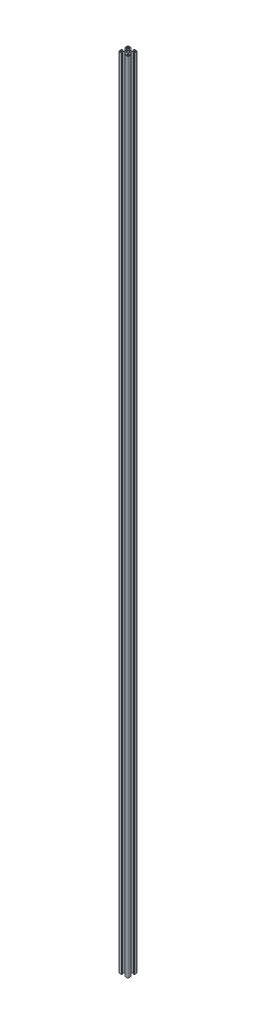
SolidWorks part; units mm, degrees
material "6063-T5"
ref_plane "前视基准面" through (0, 0, 0) normal (0, 0, 1) x (1, 0, 0)
ref_plane "上视基准面" through (0, 0, 0) normal (0, 1, 0) x (1, 0, 0)
ref_plane "右视基准面" through (0, 0, 0) normal (1, 0, 0) x (0, 0, -1)
sketch "草图3" plane through (0, 0, 0) normal (0, 1, 0) x (1, 0, 0)
  line L0 (0, 0) -> (-15, -15) construction
  line L1 (-15, -15) -> (-15, 0) construction
  line L2 (-15, 0) -> (0, 0) construction
  line L3 (-15, -12.5) -> (-15, -5.4)
  line L4 (-14.8, -5.2) -> (-14.4, -5.2)
  line L5 (-14.2, -5) -> (-14.2, -4.3)
  line L6 (-14, -4.1) -> (-13.2, -4.1)
  line L7 (-13.2, -4.1) -> (-13.2, -8.25)
  line L8 (-13.2, -8.25) -> (-9.5228, -8.25)
  line L9 (-9.5228, -8.25) -> (-5.8, -4.5272)
  line L10 (-5.8, -4.5272) -> (-5.8, 4.5272)
  line L11 (-13.2, -12.2) -> (-13.2, -11.05)
  line L12 (-12.2, -10.05) -> (-11.05, -10.05)
  line L13 (-4.5272, -5.8) -> (4.5272, -5.8)
  line L14 (-8.25, -9.5228) -> (-4.5272, -5.8)
  line L15 (-12.2, -13.2) -> (-11.05, -13.2)
  line L16 (-10.05, -12.2) -> (-10.05, -11.05)
  line L17 (-5.2, -14.8) -> (-5.2, -14.4)
  line L18 (-5, -14.2) -> (-4.3, -14.2)
  line L19 (-4.1, -14) -> (-4.1, -13.2)
  line L20 (-4.1, -13.2) -> (-8.25, -13.2)
  line L21 (-8.25, -13.2) -> (-8.25, -9.5228)
  line L22 (-12.5, -15) -> (-5.4, -15)
  line L23 (-12.5, 15) -> (-5.4, 15)
  line L24 (-8.25, 13.2) -> (-8.25, 9.5228)
  line L25 (-4.1, 13.2) -> (-8.25, 13.2)
  line L26 (-4.1, 14) -> (-4.1, 13.2)
  line L27 (-5, 14.2) -> (-4.3, 14.2)
  line L28 (-5.2, 14.8) -> (-5.2, 14.4)
  line L29 (-10.05, 12.2) -> (-10.05, 11.05)
  line L30 (-12.2, 13.2) -> (-11.05, 13.2)
  line L31 (-8.25, 9.5228) -> (-4.5272, 5.8)
  line L32 (-4.5272, 5.8) -> (4.5272, 5.8)
  line L33 (-12.2, 10.05) -> (-11.05, 10.05)
  line L34 (-13.2, 12.2) -> (-13.2, 11.05)
  line L35 (-9.5228, 8.25) -> (-5.8, 4.5272)
  line L36 (-13.2, 8.25) -> (-9.5228, 8.25)
  line L37 (-13.2, 4.1) -> (-13.2, 8.25)
  line L38 (-14, 4.1) -> (-13.2, 4.1)
  line L39 (-14.2, 5) -> (-14.2, 4.3)
  line L40 (-14.8, 5.2) -> (-14.4, 5.2)
  line L41 (-15, 12.5) -> (-15, 5.4)
  line L42 (0, 0) -> (0, -12.3268) construction
  line L43 (15, 12.5) -> (15, 5.4)
  line L44 (14.8, 5.2) -> (14.4, 5.2)
  line L45 (14.2, 5) -> (14.2, 4.3)
  line L46 (14, 4.1) -> (13.2, 4.1)
  line L47 (13.2, 4.1) -> (13.2, 8.25)
  line L48 (13.2, 8.25) -> (9.5228, 8.25)
  line L49 (9.5228, 8.25) -> (5.8, 4.5272)
  line L50 (13.2, 12.2) -> (13.2, 11.05)
  line L51 (12.2, 10.05) -> (11.05, 10.05)
  line L52 (8.25, 9.5228) -> (4.5272, 5.8)
  line L53 (12.2, 13.2) -> (11.05, 13.2)
  line L54 (10.05, 12.2) -> (10.05, 11.05)
  line L55 (5.2, 14.8) -> (5.2, 14.4)
  line L56 (5, 14.2) -> (4.3, 14.2)
  line L57 (4.1, 14) -> (4.1, 13.2)
  line L58 (4.1, 13.2) -> (8.25, 13.2)
  line L59 (8.25, 13.2) -> (8.25, 9.5228)
  line L60 (12.5, 15) -> (5.4, 15)
  line L61 (12.5, -15) -> (5.4, -15)
  line L62 (8.25, -13.2) -> (8.25, -9.5228)
  line L63 (4.1, -13.2) -> (8.25, -13.2)
  line L64 (4.1, -14) -> (4.1, -13.2)
  line L65 (5, -14.2) -> (4.3, -14.2)
  line L66 (5.2, -14.8) -> (5.2, -14.4)
  line L67 (10.05, -12.2) -> (10.05, -11.05)
  line L68 (12.2, -13.2) -> (11.05, -13.2)
  line L69 (8.25, -9.5228) -> (4.5272, -5.8)
  line L70 (12.2, -10.05) -> (11.05, -10.05)
  line L71 (13.2, -12.2) -> (13.2, -11.05)
  line L72 (5.8, -4.5272) -> (5.8, 4.5272)
  line L73 (9.5228, -8.25) -> (5.8, -4.5272)
  line L74 (13.2, -8.25) -> (9.5228, -8.25)
  line L75 (13.2, -4.1) -> (13.2, -8.25)
  line L76 (14, -4.1) -> (13.2, -4.1)
  line L77 (14.2, -5) -> (14.2, -4.3)
  line L78 (14.8, -5.2) -> (14.4, -5.2)
  line L79 (15, -12.5) -> (15, -5.4)
  circle A0 centre (0, 0) radius 3.4
  arc A1 (-12.5, 15) -> (-15, 12.5) centre (-12.5, 12.5) ccw
  arc A2 (15, 12.5) -> (12.5, 15) centre (12.5, 12.5) ccw
  arc A3 (12.5, -15) -> (15, -12.5) centre (12.5, -12.5) ccw
  arc A4 (-15, -12.5) -> (-12.5, -15) centre (-12.5, -12.5) ccw
  arc A5 (-12.2, 13.2) -> (-13.2, 12.2) centre (-12.2, 12.2) ccw
  arc A6 (-12.2, 10.05) -> (-13.2, 11.05) centre (-12.2, 11.05) cw
  arc A7 (-10.05, 11.05) -> (-11.05, 10.05) centre (-11.05, 11.05) cw
  arc A8 (-10.05, 12.2) -> (-11.05, 13.2) centre (-11.05, 12.2) ccw
  arc A9 (11.05, 10.05) -> (10.05, 11.05) centre (11.05, 11.05) cw
  arc A10 (11.05, 13.2) -> (10.05, 12.2) centre (11.05, 12.2) ccw
  arc A11 (13.2, 12.2) -> (12.2, 13.2) centre (12.2, 12.2) ccw
  arc A12 (13.2, 11.05) -> (12.2, 10.05) centre (12.2, 11.05) cw
  arc A13 (12.2, -10.05) -> (13.2, -11.05) centre (12.2, -11.05) cw
  arc A14 (10.05, -11.05) -> (11.05, -10.05) centre (11.05, -11.05) cw
  arc A15 (10.05, -12.2) -> (11.05, -13.2) centre (11.05, -12.2) ccw
  arc A16 (12.2, -13.2) -> (13.2, -12.2) centre (12.2, -12.2) ccw
  arc A17 (-13.2, -11.05) -> (-12.2, -10.05) centre (-12.2, -11.05) cw
  arc A18 (-11.05, -10.05) -> (-10.05, -11.05) centre (-11.05, -11.05) cw
  arc A19 (-11.05, -13.2) -> (-10.05, -12.2) centre (-11.05, -12.2) ccw
  arc A20 (-13.2, -12.2) -> (-12.2, -13.2) centre (-12.2, -12.2) ccw
  arc A21 (-15, -5.4) -> (-14.8, -5.2) centre (-14.8, -5.4) cw
  arc A22 (-14.4, -5.2) -> (-14.2, -5) centre (-14.4, -5) ccw
  arc A23 (-14.2, -4.3) -> (-14, -4.1) centre (-14, -4.3) cw
  arc A24 (-14, 4.1) -> (-14.2, 4.3) centre (-14, 4.3) cw
  arc A25 (-14.2, 5) -> (-14.4, 5.2) centre (-14.4, 5) ccw
  arc A26 (-14.8, 5.2) -> (-15, 5.4) centre (-14.8, 5.4) cw
  arc A27 (-5.4, 15) -> (-5.2, 14.8) centre (-5.4, 14.8) cw
  arc A28 (-5, 14.2) -> (-5.2, 14.4) centre (-5, 14.4) cw
  arc A29 (-4.1, 14) -> (-4.3, 14.2) centre (-4.3, 14) ccw
  arc A30 (5.2, 14.8) -> (5.4, 15) centre (5.4, 14.8) cw
  arc A31 (5.2, 14.4) -> (5, 14.2) centre (5, 14.4) cw
  arc A32 (4.3, 14.2) -> (4.1, 14) centre (4.3, 14) ccw
  arc A33 (15, 5.4) -> (14.8, 5.2) centre (14.8, 5.4) cw
  arc A34 (14.4, 5.2) -> (14.2, 5) centre (14.4, 5) ccw
  arc A35 (14.2, 4.3) -> (14, 4.1) centre (14, 4.3) cw
  arc A36 (14, -4.1) -> (14.2, -4.3) centre (14, -4.3) cw
  arc A37 (14.2, -5) -> (14.4, -5.2) centre (14.4, -5) ccw
  arc A38 (14.8, -5.2) -> (15, -5.4) centre (14.8, -5.4) cw
  arc A39 (5.4, -15) -> (5.2, -14.8) centre (5.4, -14.8) cw
  arc A40 (5, -14.2) -> (5.2, -14.4) centre (5, -14.4) cw
  arc A41 (4.1, -14) -> (4.3, -14.2) centre (4.3, -14) ccw
  arc A42 (-5.2, -14.4) -> (-5, -14.2) centre (-5, -14.4) cw
  arc A43 (-4.3, -14.2) -> (-4.1, -14) centre (-4.3, -14) ccw
  arc A44 (-5.2, -14.8) -> (-5.4, -15) centre (-5.4, -14.8) cw
  point P38 (-5.8, 0)
  point P46 (0, 5.8)
  point P47 (0, -5.8)
  point P83 (5.8, 0)
  point P87 (-15, 15)
  point P90 (15, 15)
  point P93 (15, -15)
  point P99 (-13.2, 13.2)
  point P102 (-13.2, 10.05)
  point P105 (-10.05, 10.05)
  point P108 (-10.05, 13.2)
  point P111 (10.05, 10.05)
  point P114 (10.05, 13.2)
  point P117 (13.2, 13.2)
  point P120 (13.2, 10.05)
  point P123 (13.2, -10.05)
  point P126 (10.05, -10.05)
  point P129 (10.05, -13.2)
  point P132 (13.2, -13.2)
  point P135 (-13.2, -10.05)
  point P138 (-10.05, -10.05)
  point P141 (-10.05, -13.2)
  point P144 (-13.2, -13.2)
  point P147 (-15, -5.2)
  point P150 (-14.2, -5.2)
  point P153 (-14.2, -4.1)
  point P156 (-14.2, 4.1)
  point P159 (-14.2, 5.2)
  point P162 (-15, 5.2)
  point P165 (-5.2, 15)
  point P168 (-5.2, 14.2)
  point P171 (-4.1, 14.2)
  point P174 (5.2, 15)
  point P177 (5.2, 14.2)
  point P180 (4.1, 14.2)
  point P183 (15, 5.2)
  point P186 (14.2, 5.2)
  point P189 (14.2, 4.1)
  point P192 (14.2, -4.1)
  point P195 (14.2, -5.2)
  point P198 (15, -5.2)
  point P201 (5.2, -15)
  point P204 (5.2, -14.2)
  point P207 (4.1, -14.2)
  point P210 (-5.2, -14.2)
  point P213 (-4.1, -14.2)
  point P216 (-5.2, -15)
  dimension "D11" = 6.8
  dimension "D12" = 2.5
  dimension "D13" = 1
  dimension "D14" = 0.2
  dimension "D2" = 15
  dimension "D3" = 4.1
  dimension "D4" = 5.2
  dimension "D5" = 0.8
  dimension "D6" = 1.8
  dimension "D7" = 9.2
  dimension "D8" = 8.25
  dimension "D9" = 0.9
  dimension "D10" = 1.8
extrude "凸台-拉伸1" add sketch "草图3" along normal blind 2554
